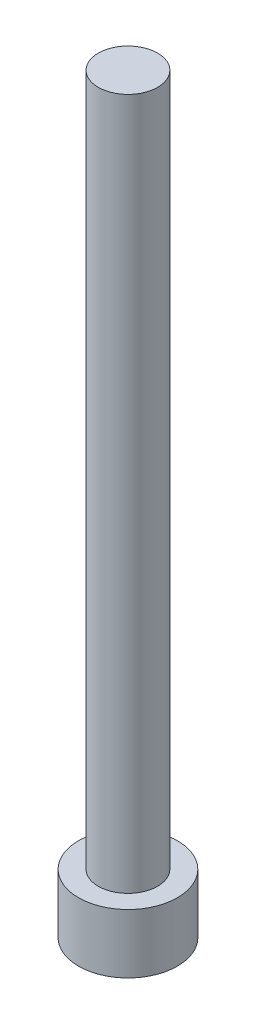
SolidWorks part; units mm, degrees
ref_plane "前视基准面" through (0, 0, 0) normal (0, 0, 1) x (1, 0, 0)
ref_plane "上视基准面" through (0, 0, 0) normal (0, 1, 0) x (1, 0, 0)
ref_plane "右视基准面" through (0, 0, 0) normal (1, 0, 0) x (0, 0, -1)
sketch "草图1" plane through (0, 0, 0) normal (0, 1, 0) x (1, 0, 0)
  circle A0 centre (0, 0) radius 2.5
  dimension "D1" = 5
extrude "凸台-拉伸1" add sketch "草图1" along normal blind 3
sketch "草图2" plane through (0, 3, 0) normal (0, 1, 0) x (1, 0, 0)
  circle A0 centre (0, 0) radius 1.5
extrude "凸台-拉伸2" add sketch "草图2" along normal blind 35
sketch "草图3" plane through (0, 0, 0) normal (0, -1, 0) x (1, 0, 0)
  line L1 (1.425, 0) -> (0.7125, 1.2341)
  line L2 (0.7125, 1.2341) -> (-0.7125, 1.2341)
  line L3 (-0.7125, 1.2341) -> (-1.425, 0)
  line L4 (-1.425, 0) -> (-0.7125, -1.2341)
  line L5 (-0.7125, -1.2341) -> (0.7125, -1.2341)
  line L6 (0.7125, -1.2341) -> (1.425, 0)
  circle A0 centre (0, 0) radius 1.2341 construction
extrude "切除-拉伸1" cut sketch "草图3" against normal blind 1.65
